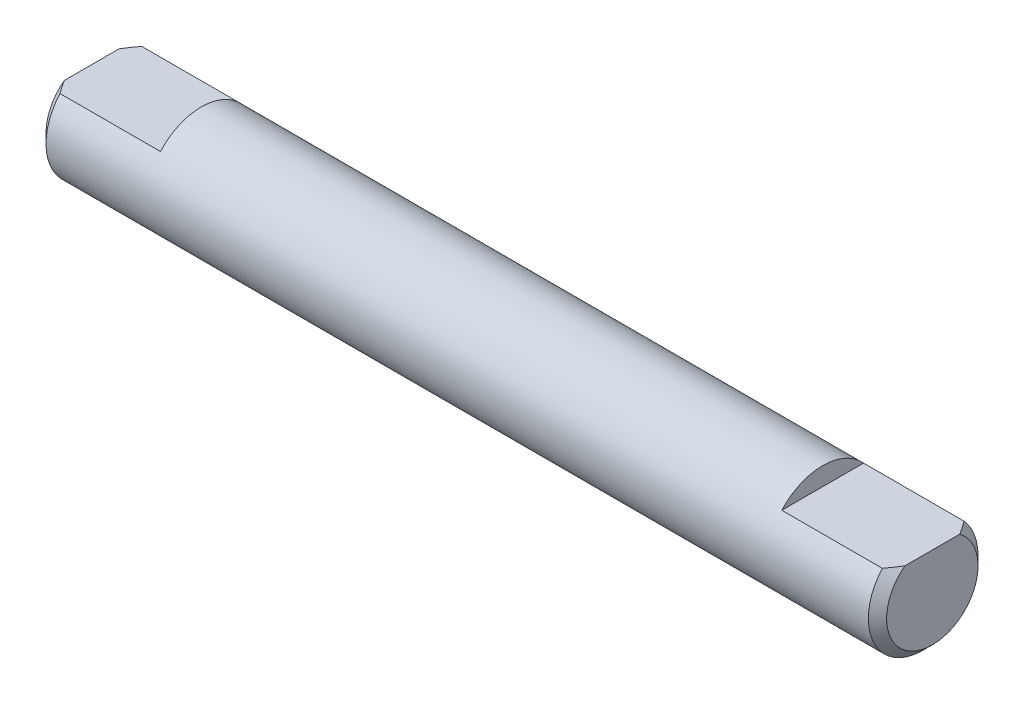
SolidWorks part; units mm, degrees
ref_plane "Front Plane" through (0, 0, 0) normal (0, 0, 1) x (1, 0, 0)
ref_plane "Top Plane" through (0, 0, 0) normal (0, 1, 0) x (1, 0, 0)
ref_plane "Right Plane" through (0, 0, 0) normal (1, 0, 0) x (0, 0, -1)
sketch "Sketch1" plane through (0, 0, 0) normal (1, 0, 0) x (0, 0, -1)
  circle A0 centre (0, 0) radius 3
  dimension "D1" = 6
extrude "Boss-Extrude1" add sketch "Sketch1" along normal mid plane 46
chamfer "Chamfer1" distance 0.5 angle 45 2 edges at (-23, 0, -3) (23, 0, -3)
sketch "Sketch2" plane through (23, 0, 0) normal (1, 0, 0) x (0, 0, -1)
  line L0 (-2.2361, 2) -> (2.2361, 2)
  circle A1 centre (0, 0) radius 3
  arc A2 (2.2361, 2) -> (-2.2361, 2) centre (0, 0) ccw
  dimension "D2" = 2
  dimension "D1" = 0
extrude "Cut-Extrude1" cut sketch "Sketch2" against normal blind 6
mirror "Mirror1" about plane through (0, 0, 0) normal (1, 0, 0) of "Cut-Extrude1"
